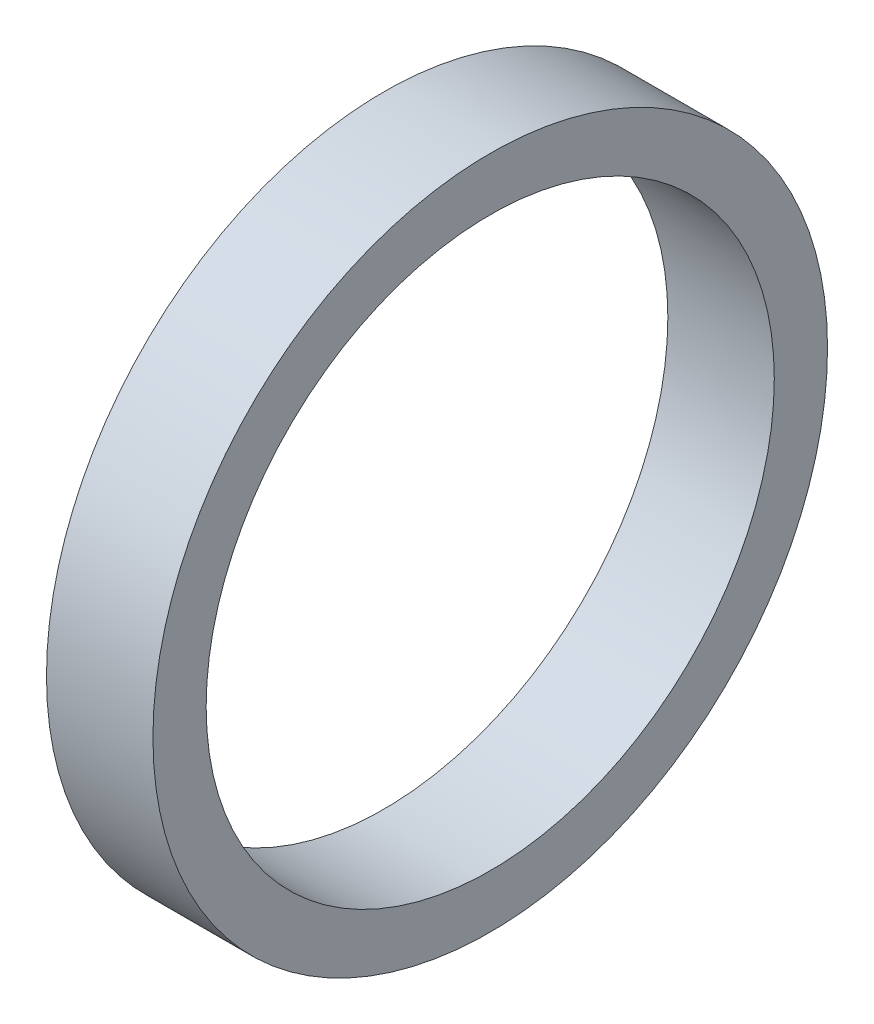
SolidWorks part; units mm, degrees
ref_plane "Alzado" through (0, 0, 0) normal (0, 0, 1) x (1, 0, 0)
ref_plane "Planta" through (0, 0, 0) normal (0, 1, 0) x (1, 0, 0)
ref_plane "Vista lateral" through (0, 0, 0) normal (1, 0, 0) x (0, 0, -1)
sketch "Croquis1" plane through (0, 0, 0) normal (0, 1, 0) x (1, 0, 0)
  line L0 (-20.7851, 0) -> (20.7851, 0) construction
  line L1 (0, 10.675) -> (-4, 10.675)
  line L2 (-4, 10.675) -> (-4, 12.675)
  line L3 (-4, 12.675) -> (0, 12.675)
  line L4 (0, 12.675) -> (0, 10.675)
  point P3 (0, 0)
  dimension "D1" = 25.35
  dimension "D2" = 21.35
  dimension "D3" = 4
  dimension "D4" = 0
revolve "Revolución1" add sketch "Croquis1" angle 360 about L0
